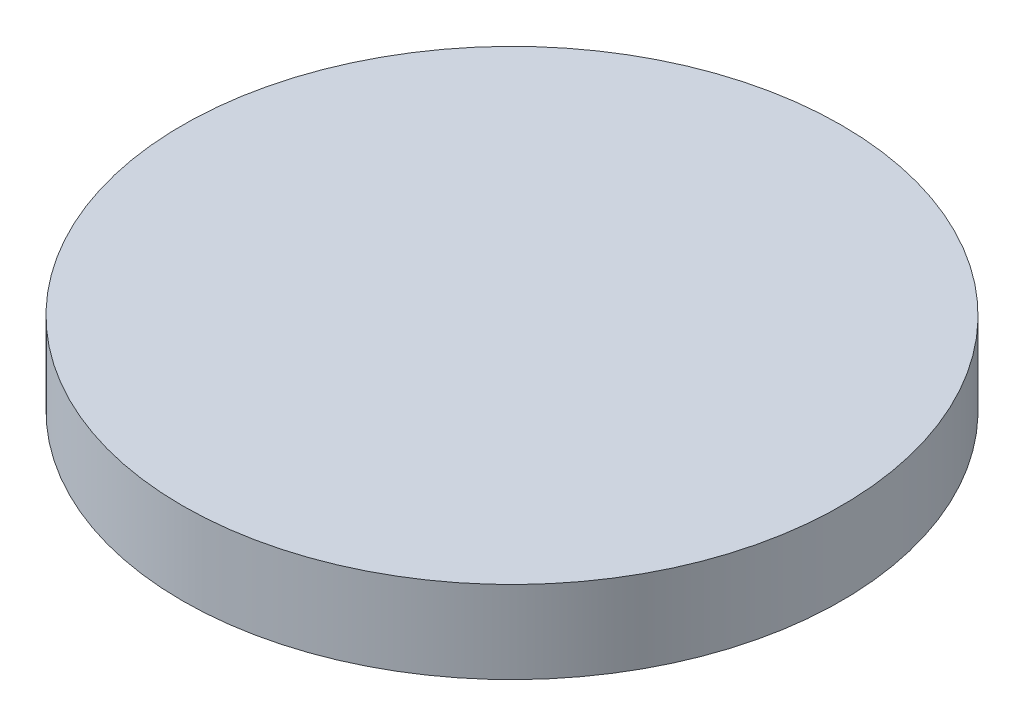
SolidWorks part; units mm, degrees
ref_plane "Front Plane" through (0, 0, 0) normal (0, 0, 1) x (1, 0, 0)
ref_plane "Top Plane" through (0, 0, 0) normal (0, 1, 0) x (1, 0, 0)
ref_plane "Right Plane" through (0, 0, 0) normal (1, 0, 0) x (0, 0, -1)
sketch "Sketch1" plane through (0, 0, 0) normal (0, 1, 0) x (1, 0, 0)
  circle A0 centre (-55.523, 32.2611) radius 50.8
  dimension "D1" = 101.6
extrude "Boss-Extrude1" add sketch "Sketch1" along normal blind 12.7
